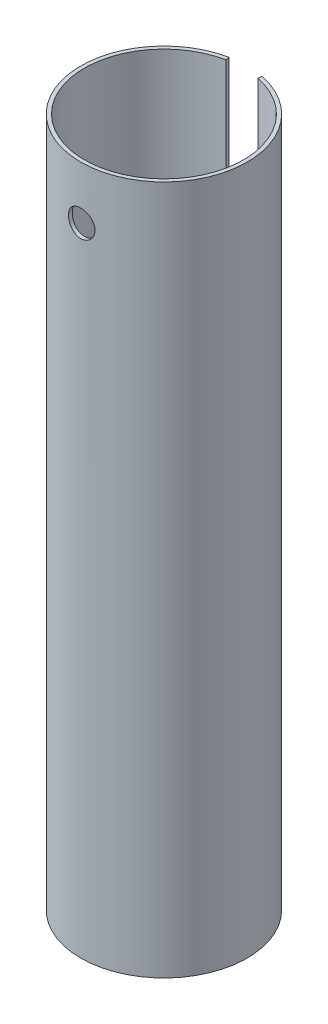
SolidWorks part; units mm, degrees
material "Латунь"
ref_plane "Спереди" through (0, 0, 0) normal (0, 0, 1) x (1, 0, 0)
ref_plane "Сверху" through (0, 0, 0) normal (0, 1, 0) x (1, 0, 0)
ref_plane "Справа" through (0, 0, 0) normal (1, 0, 0) x (0, 0, -1)
sketch "Эскиз1" plane through (0, 0, 0) normal (0, 1, 0) x (1, 0, 0)
  line L0 (-0.314, 1.5383) -> (-0.3, 1.4697)
  line L1 (0.314, 1.5383) -> (0.3, 1.4697)
  arc A0 (0.3, 1.4697) -> (-0.3, 1.4697) centre (0, 0) cw
  arc A1 (0.314, 1.5383) -> (-0.314, 1.5383) centre (0, 0) cw
  dimension "D2" = 1.5
  dimension "D1" = 0.6
  dimension "D3" = 0.07
extrude "Бобышка-Вытянуть1" add sketch "Эскиз1" along normal blind 13
sketch "Эскиз2" plane through (0, 0, 0) normal (0, 0, 1) x (1, 0, 0)
  line L0 (-1.57, 0) -> (1.57, 0) construction
  circle A0 centre (0, 12) radius 0.25
  dimension "D1" = 0.5
  dimension "D2" = 12
extrude "Вырез-Вытянуть1" cut sketch "Эскиз2" along normal through all
